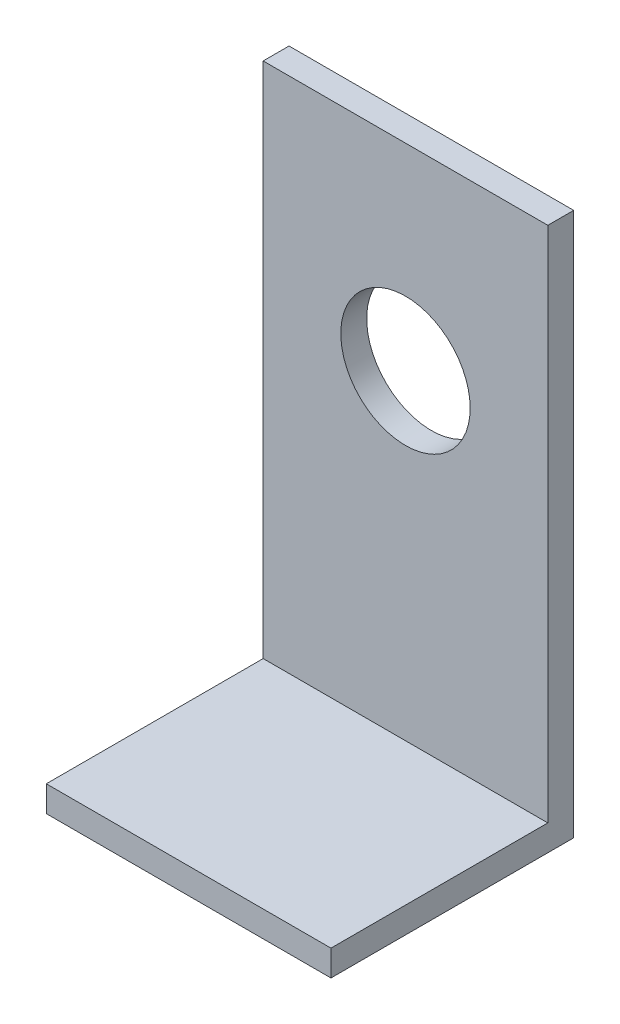
SolidWorks part; units mm, degrees
ref_plane "Alzado" through (0, 0, 0) normal (0, 0, 1) x (1, 0, 0)
ref_plane "Planta" through (0, 0, 0) normal (0, 1, 0) x (1, 0, 0)
ref_plane "Vista lateral" through (0, 0, 0) normal (1, 0, 0) x (0, 0, -1)
sketch "Croquis1" plane through (0, 0, 0) normal (0, 0, 1) x (1, 0, 0)
  line L0 (0, 0) -> (0, 105) construction
  line L1 (0, 105) -> (27.5, 105)
  line L2 (27.5, 105) -> (27.5, 0)
  line L3 (27.5, 0) -> (-27.5, 0)
  line L4 (-27.5, 0) -> (-27.5, 105)
  line L5 (-27.5, 105) -> (0, 105)
  circle A0 centre (0, 66.9) radius 12.5
  dimension "D3" = 25
  dimension "D1" = 105
  dimension "D2" = 55
  dimension "D4" = 66.9
extrude "Saliente-Extruir1" add sketch "Croquis1" along normal blind 5
sketch "Croquis2" plane through (0, 0, 5) normal (0, 0, 1) x (1, 0, 0)
  line L0 (-27.5, 0) -> (-27.5, 5)
  line L1 (-27.5, 105) -> (-27.5, 0) construction
  line L2 (-27.5, 5) -> (27.5, 5)
  line L3 (27.5, 0) -> (27.5, 105) construction
  line L4 (27.5, 5) -> (27.5, 0)
  line L5 (27.5, 0) -> (-27.5, 0)
  dimension "D1" = 5
extrude "Saliente-Extruir2" add sketch "Croquis2" along normal blind 41.9
